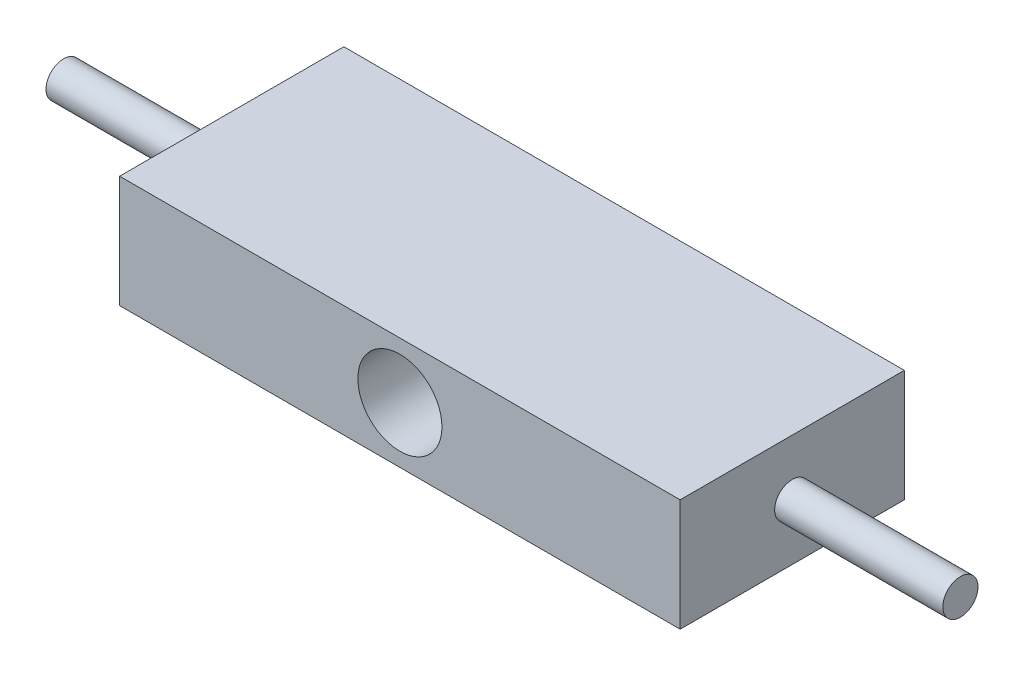
SolidWorks part; units mm, degrees
ref_plane "Front Plane" through (0, 0, 0) normal (0, 0, 1) x (1, 0, 0)
ref_plane "Top Plane" through (0, 0, 0) normal (0, 1, 0) x (1, 0, 0)
ref_plane "Right Plane" through (0, 0, 0) normal (1, 0, 0) x (0, 0, -1)
sketch "Sketch1" plane through (0, 0, 0) normal (0, 0, 1) x (1, 0, 0)
  line L1 (-31.75, 6.35) -> (31.75, 6.35)
  line L2 (-31.75, 6.35) -> (-31.75, -6.35)
  line L3 (-31.75, -6.35) -> (31.75, -6.35)
  line L4 (31.75, 6.35) -> (31.75, -6.35)
  line L5 (-31.75, 6.35) -> (31.75, -6.35) construction
  line L6 (-31.75, -6.35) -> (31.75, 6.35) construction
  circle A0 centre (0, 0) radius 4.7625
  point P0 (0, 0)
  dimension "D3" = 9.525
  dimension "D1" = 12.7
  dimension "D2" = 63.5
extrude "Boss-Extrude1" add sketch "Sketch1" against normal blind 25.4
sketch "Sketch2" plane through (31.75, 0, 0) normal (1, 0, 0) x (0, 0, -1)
  line L0 (0, 6.35) -> (25.4, -6.35) construction
  line L1 (25.4, 6.35) -> (0, -6.35) construction
  line L4 (0, 6.35) -> (0, -6.35)
  line L5 (0, -6.35) -> (25.4, -6.35)
  line L6 (25.4, -6.35) -> (25.4, 6.35)
  line L7 (25.4, 6.35) -> (0, 6.35)
  line L8 (0, 6.35) -> (0, -6.35)
  line L9 (0, -6.35) -> (25.4, -6.35)
  line L10 (25.4, -6.35) -> (25.4, 6.35)
  line L11 (25.4, 6.35) -> (0, 6.35)
  circle A0 centre (12.7, 0) radius 1.9939
  dimension "D2" = 3.9878
  dimension "D1" = 0
extrude "Boss-Extrude2" add sketch "Sketch2" along normal blind 19.05 contours A0
sketch "Sketch3" plane through (-31.75, 0, 0) normal (-1, 0, 0) x (0, 0, 1)
  line L0 (0, 6.35) -> (-25.4, -6.35) construction
  line L1 (-25.4, 6.35) -> (0, -6.35) construction
  line L2 (0, 6.35) -> (-25.4, -6.35)
  line L3 (-25.4, 6.35) -> (0, -6.35)
  line L4 (0, -6.35) -> (0, 6.35)
  line L5 (-25.4, -6.35) -> (0, -6.35)
  line L6 (-25.4, 6.35) -> (-25.4, -6.35)
  line L7 (0, 6.35) -> (-25.4, 6.35)
  line L8 (0, -6.35) -> (0, 6.35)
  line L9 (-25.4, -6.35) -> (0, -6.35)
  line L10 (-25.4, 6.35) -> (-25.4, -6.35)
  line L11 (0, 6.35) -> (-25.4, 6.35)
  circle A0 centre (-12.7, 0) radius 1.9939 construction
  circle A1 centre (-12.7, 0) radius 1.9939
  dimension "D1" = 0
extrude "Boss-Extrude3" add sketch "Sketch3" along normal blind 19.05 contours A1
